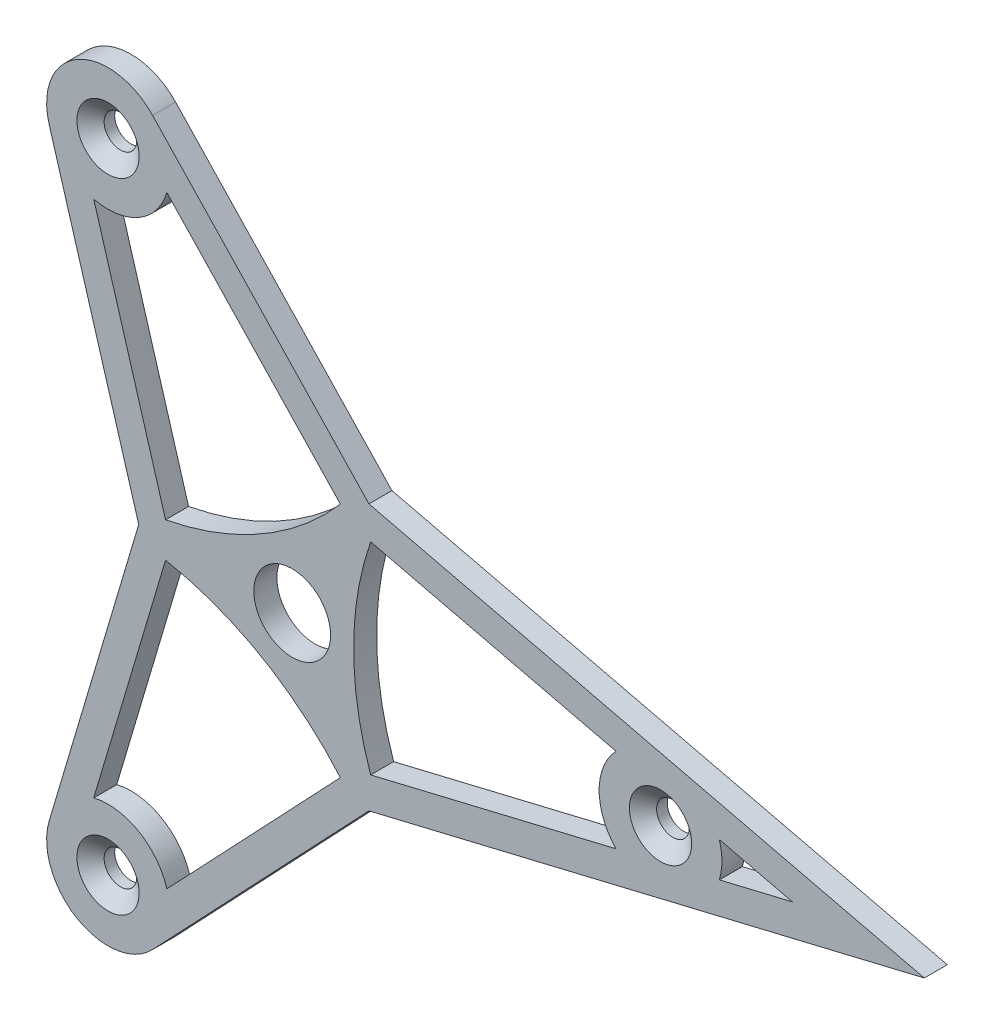
SolidWorks part; units mm, degrees
material "PVC 0.007 Plasticized"
ref_plane "Front Plane" through (0, 0, 0) normal (0, 0, 1) x (1, 0, 0)
ref_plane "Top Plane" through (0, 0, 0) normal (0, 1, 0) x (1, 0, 0)
ref_plane "Right Plane" through (0, 0, 0) normal (1, 0, 0) x (0, 0, -1)
sketch "Sketch1" plane through (0, 0, 0) normal (0, 0, 1) x (1, 0, 0)
  line L0 (93.017, 0) -> (-97.9083, 0) construction
  line L1 (0, 0) -> (-38.1, 65.9911) construction
  line L2 (0, 0) -> (-38.1, -65.9911) construction
  line L3 (0, 0) -> (38.1, 65.9911) construction
  line L4 (0, 0) -> (38.1, -65.9911) construction
  line L5 (-31.75, 0) -> (-50.2745, 62.3755)
  line L6 (-31.75, 0) -> (-50.2745, -62.3755)
  line L7 (15.875, -27.4963) -> (-28.8816, -74.7267)
  line L8 (15.875, -27.4963) -> (79.156, -12.3512)
  line L9 (15.875, 27.4963) -> (78.9112, 12.4098)
  line L10 (15.875, 27.4963) -> (-28.8816, 74.7267)
  line L11 (78.9112, 12.4098) -> (130.7632, 0)
  line L12 (79.156, -12.3512) -> (130.7632, 0)
  line L13 (9.9682, 24.4978) -> (-25.9255, 62.3755)
  line L14 (16.2316, 20.8816) -> (66.9816, 8.7356)
  line L15 (88.3745, 3.6156) -> (103.4816, 0)
  line L16 (88.3745, -3.6156) -> (103.4816, 0)
  line L17 (16.2316, -20.8816) -> (66.9816, -8.7356)
  line L18 (9.9682, -24.4978) -> (-25.9255, -62.3755)
  line L19 (-26.1998, -3.6162) -> (-41.056, -53.6399)
  line L20 (-26.1998, 3.6162) -> (-41.056, 53.6399)
  line L21 (-25.1259, 0) -> (-44.1872, -64.1833) construction
  line L22 (12.5629, -21.7597) -> (-33.4908, -70.3589) construction
  line L23 (77.678, -6.1756) -> (103.4816, 0) construction
  line L24 (77.4332, 6.2342) -> (103.4816, 0) construction
  line L25 (12.5629, 21.7597) -> (77.4332, 6.2342) construction
  line L27 (12.5629, -21.7597) -> (77.678, -6.1756) construction
  line L28 (12.5629, 21.7597) -> (-33.4908, 70.3589) construction
  line L29 (-25.1259, 0) -> (-44.1872, 64.1833) construction
  circle A0 centre (0, 0) radius 7.9375
  circle A1 centre (0, 0) radius 31.75 construction
  circle A2 centre (0, 0) radius 12.7 construction
  circle A3 centre (0, 0) radius 76.2 construction
  arc A4 (66.9816, 8.7356) -> (66.9816, -8.7356) centre (76.2, 0) ccw
  arc A6 (-50.2745, -62.3755) -> (-28.8816, -74.7267) centre (-38.1, -65.9911) ccw
  arc A7 (-28.8816, 74.7267) -> (-50.2745, 62.3755) centre (-38.1, 65.9911) ccw
  arc A8 (-25.9255, -62.3755) -> (-41.056, -53.6399) centre (-38.1, -65.9911) ccw
  arc A9 (88.3745, -3.6156) -> (88.3745, 3.6156) centre (76.2, 0) ccw
  arc A10 (-41.056, 53.6399) -> (-25.9255, 62.3755) centre (-38.1, 65.9911) ccw
  arc A12 (-32.5617, -2.7331) -> (13.9139, -29.5658) centre (-38.1, -65.9911) ccw construction
  arc A14 (13.9139, 29.5658) -> (-32.5617, 2.7331) centre (-38.1, 65.9911) ccw construction
  arc A19 (16.2316, 20.8816) -> (16.2316, -20.8816) centre (76.2, 0) ccw
  arc A20 (-26.1998, 3.6162) -> (9.9682, 24.4978) centre (-38.1, 65.9911) ccw
  arc A21 (18.6478, -26.8327) -> (18.6478, 26.8327) centre (76.2, 0) ccw construction
  arc A22 (9.9682, -24.4978) -> (-26.1998, -3.6162) centre (-38.1, -65.9911) ccw
  point P16 (0, 0)
  dimension "D1" = 15.875
  dimension "D2" = 63.5
  dimension "D3" = 25.4
  dimension "D4" = 152.4
  dimension "D5" = 25.4
  dimension "D6" = 3
  dimension "D7" = 60
  dimension "D8" = 60
  dimension "D9" = 6.35
  dimension "D10" = 6.35
extrude "Boss-Extrude1" add sketch "Sketch1" against normal blind 4.7625
hole_wizard "CSK for 1/4 Flat Head Machine Screw (100)1" positions "Sketch2" profile "Sketch3" countersink size "1/4" standard "ANSI Inch" end condition through all
sketch "Sketch2" plane through (0, 0, 0) normal (0, 0, 1) x (1, 0, 0)
  point P0 (76.2, 0)
  point P3 (-38.1, 65.9911)
  point P6 (-38.1, -65.9911)
sketch "Sketch3" plane through (76.2, 0, 0) normal (1, 0, 0) x (0, -1, 0)
  line L0 (0, 0) -> (0, 4.7625)
  line L1 (0, 4.7625) -> (3.3782, 4.7625)
  line L2 (3.3782, 4.7625) -> (3.3782, 2.5682)
  line L3 (3.3782, 2.5682) -> (6.4389, 0)
  line L5 (6.4389, 0) -> (0, 0)
  line L6 (-3.3782, 2.5682) -> (-6.4389, 0) construction
  line L11 (0, -6.35) -> (0, 107.95) construction
  dimension "Thru Hole Dia." = 6.7564
  dimension "Thru Hole Depth" = 4.7625
  dimension "Near C'Sink Dia." = 12.8778
  dimension "Near C'Sink Angle" = 100
